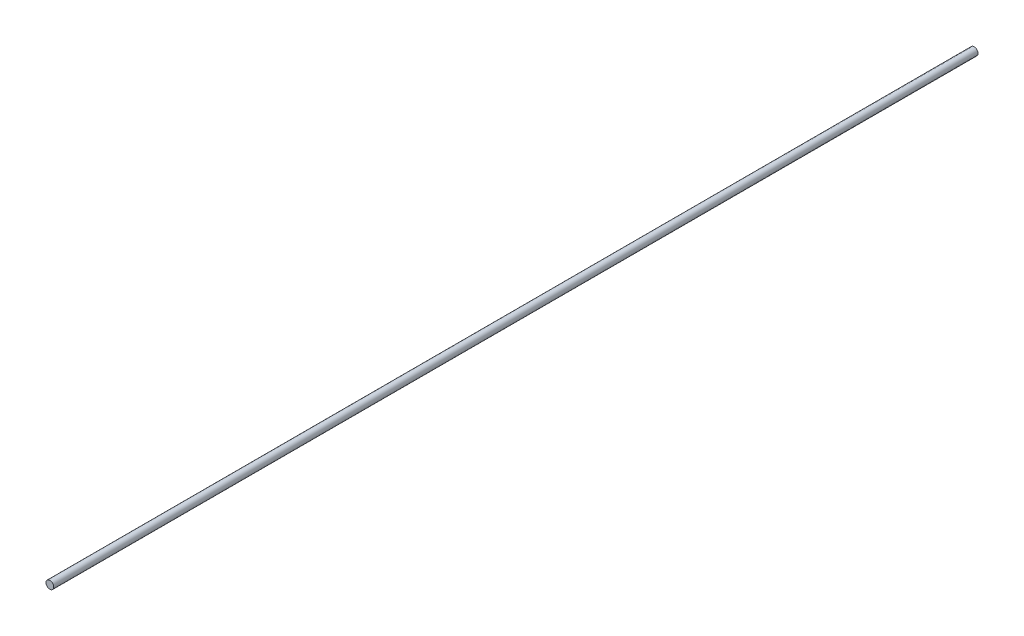
SolidWorks part; units mm, degrees
ref_plane "Front Plane" through (0, 0, 0) normal (0, 0, 1) x (1, 0, 0)
ref_plane "Top Plane" through (0, 0, 0) normal (0, 1, 0) x (1, 0, 0)
ref_plane "Right Plane" through (0, 0, 0) normal (1, 0, 0) x (0, 0, -1)
sketch "Sketch1" plane through (0, 0, 0) normal (0, 0, 1) x (1, 0, 0)
  circle A0 centre (0, 0) radius 3.175
  dimension "D1" = 6.35
extrude "Boss-Extrude1" add sketch "Sketch1" along normal blind 762
